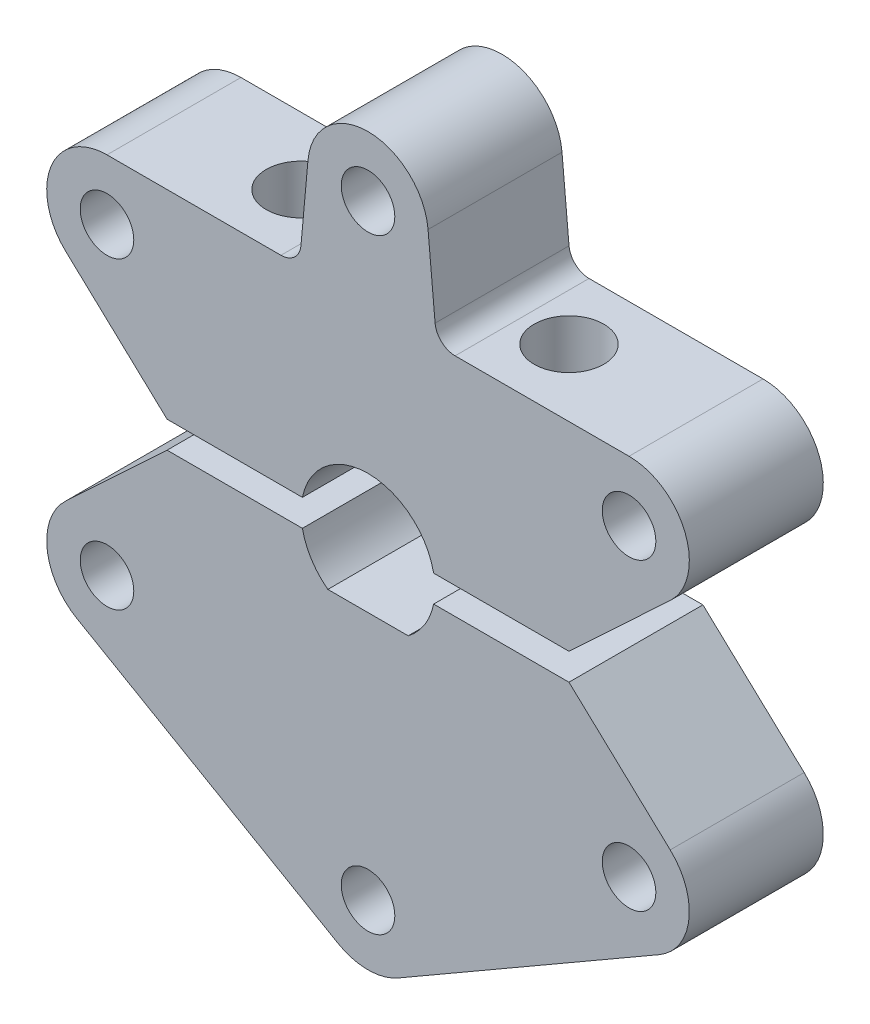
SolidWorks part; units mm, degrees
material "6061 合金"
ref_plane "前视基准面" through (0, 0, 0) normal (0, 0, 1) x (1, 0, 0)
ref_plane "上视基准面" through (0, 0, 0) normal (0, 1, 0) x (1, 0, 0)
ref_plane "右视基准面" through (0, 0, 0) normal (1, 0, 0) x (0, 0, -1)
sketch "草图1" plane through (0, 0, 0) normal (0, 0, 1) x (1, 0, 0)
  line L0 (0, 22.5) -> (0, 22.6) construction
  line L1 (0, 22.5) -> (-19.4856, 11.25) construction
  line L2 (-19.4856, 11.25) -> (-19.4856, -11.25) construction
  line L3 (-19.4856, -11.25) -> (0, -22.5) construction
  line L4 (0, -22.5) -> (19.4856, -11.25) construction
  line L5 (19.4856, -11.25) -> (19.4856, 11.25) construction
  line L6 (19.4856, 11.25) -> (0, 22.5) construction
  line L7 (-19.4856, 11.25) -> (-19.4856, 11.35) construction
  line L8 (19.4856, 11.25) -> (19.4856, 11.35) construction
  line L9 (-19.4856, -11.25) -> (-19.4856, -11.35) construction
  line L10 (0, -22.5) -> (0, -22.6) construction
  line L11 (19.4856, -11.25) -> (19.4856, -11.35) construction
  line L12 (-3, -4) -> (3, -4)
  line L13 (-15, 1) -> (-22.5579, 8.062)
  line L14 (-19.4856, 15.85) -> (-6.5, 15.85)
  line L15 (-5.0061, 17.2147) -> (-4.4817, 23.0059)
  line L16 (4.4817, 23.0059) -> (5.0061, 17.2147)
  line L17 (6.5, 15.85) -> (19.4856, 15.85)
  line L18 (22.5579, 8.062) -> (15, 1)
  line L19 (15, 1) -> (4.899, 1)
  line L20 (-5.1297, 15.85) -> (5.1297, 15.85) construction
  line L21 (-15, -1) -> (-22.5579, -8.062)
  line L22 (-4.899, 1) -> (-15, 1)
  line L23 (-21.7356, -15.2471) -> (-2.25, -26.4971)
  line L24 (2.25, -26.4971) -> (21.7356, -15.2471)
  line L25 (22.5579, -8.062) -> (15, -1)
  line L26 (15, -1) -> (4.899, -1)
  line L27 (-4.899, -1) -> (-15, -1)
  circle A0 centre (0, 0) radius 22.5 construction
  circle A1 centre (-19.4856, 11.35) radius 2
  circle A2 centre (0, 22.6) radius 2
  circle A3 centre (19.4856, 11.35) radius 2
  circle A4 centre (-19.4856, -11.35) radius 2
  circle A5 centre (0, -22.6) radius 2
  circle A6 centre (19.4856, -11.35) radius 2
  arc A7 (3, -4) -> (4.899, -1) centre (0, 0) ccw
  arc A8 (19.4856, 15.85) -> (22.5579, 8.062) centre (19.4856, 11.35) cw
  arc A9 (-22.5579, 8.062) -> (-19.4856, 15.85) centre (-19.4856, 11.35) cw
  arc A10 (-4.4817, 23.0059) -> (4.4817, 23.0059) centre (0, 22.6) cw
  arc A11 (5.0061, 17.2147) -> (6.5, 15.85) centre (6.5, 17.35) ccw
  arc A12 (-6.5, 15.85) -> (-5.0061, 17.2147) centre (-6.5, 17.35) ccw
  arc A13 (21.7356, -15.2471) -> (22.5579, -8.062) centre (19.4856, -11.35) ccw
  arc A14 (-2.25, -26.4971) -> (2.25, -26.4971) centre (0, -22.6) ccw
  arc A15 (-22.5579, -8.062) -> (-21.7356, -15.2471) centre (-19.4856, -11.35) ccw
  arc A16 (-4.899, -1) -> (-3, -4) centre (0, 0) ccw
  arc A17 (4.899, 1) -> (-4.899, 1) centre (0, 0) ccw
  dimension "D1" = 45
  dimension "D2" = 4
  dimension "D4" = 5
  dimension "D6" = 4.5
  dimension "D10" = 1.5
  dimension "D11" = 4.5
  dimension "D3" = 0.1
  dimension "D5" = 4
  dimension "D7" = 13
  dimension "D8" = 30
  dimension "D9" = 1
  dimension "D12" = 1
extrude "凸台-拉伸1" add sketch "草图1" along normal blind 10
cosmetic thread "装饰螺纹线3" parameters "D2"=5
cosmetic thread "装饰螺纹线4" parameters "D2"=5
cosmetic thread "装饰螺纹线5" parameters "D2"=5
cosmetic thread "装饰螺纹线6" parameters "D2"=5
cosmetic thread "装饰螺纹线7" parameters "D2"=5
cosmetic thread "装饰螺纹线8" parameters "D2"=5
sketch "草图2" plane through (0, 15.85, 0) normal (0, 1, 0) x (1, 0, 0)
  line L0 (-10, -5) -> (10, -5) construction
  line L2 (0, 0) -> (0, -5) construction
  line L3 (0, -5) -> (0, -10) construction
  line L4 (-4.4817, -10) -> (4.4817, -10) construction
  circle A0 centre (-10, -5) radius 2.6
  circle A1 centre (10, -5) radius 2.6
  dimension "D2" = 5.2
  dimension "D1" = 20
extrude "切除-拉伸1" cut sketch "草图2" against normal up to surface (14.85 mm away) up to face at (-9.9495, 1, 5)
sketch "草图3" plane through (0, 15.85, 0) normal (0, 1, 0) x (1, 0, 0)
  circle A0 centre (-10, -5) radius 2
  circle A1 centre (10, -5) radius 2
  dimension "D1" = 4
extrude "切除-拉伸2" cut sketch "草图3" against normal through all
cosmetic thread "装饰螺纹线1" parameters "D2"=5
cosmetic thread "装饰螺纹线2" parameters "D2"=5
